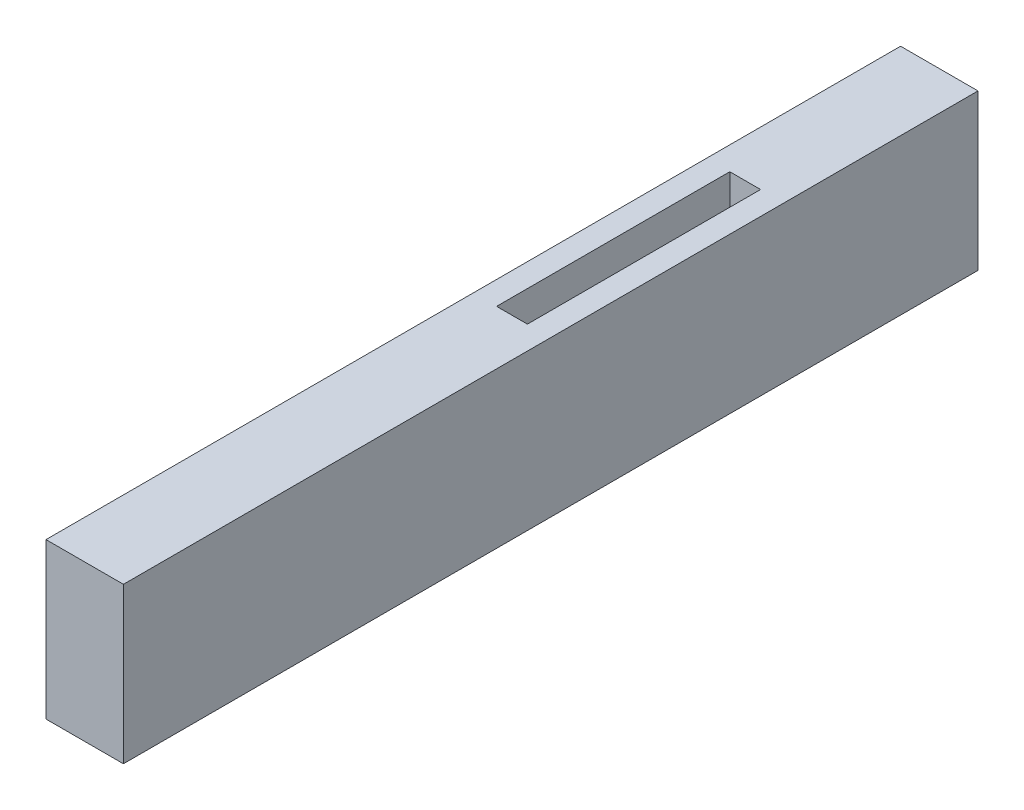
SolidWorks part; units mm, degrees
ref_plane "Front Plane" through (0, 0, 0) normal (0, 0, 1) x (1, 0, 0)
ref_plane "Top Plane" through (0, 0, 0) normal (0, 1, 0) x (1, 0, 0)
ref_plane "Right Plane" through (0, 0, 0) normal (1, 0, 0) x (0, 0, -1)
sketch "Sketch1" plane through (0, 0, 0) normal (0, 1, 0) x (1, 0, 0)
  line L0 (-14.2964, 30.5297) -> (-9.3157, 30.5297)
  line L1 (-9.3157, 30.5297) -> (-9.3157, -24.4422)
  line L2 (-9.3157, -24.4422) -> (-14.2964, -24.4422)
  line L3 (-14.2964, -24.4422) -> (-14.2964, 30.5297)
extrude "Boss-Extrude1" add sketch "Sketch1" along normal blind 10
sketch "Sketch2" plane through (0, 10, 0) normal (0, 1, 0) x (1, 0, 0)
  line L4 (-12.7964, 3.0437) -> (-10.8157, 3.0437)
  line L5 (-12.7964, 18.0437) -> (-10.8157, 18.0437)
  line L8 (-12.7964, 29.0297) -> (-12.7964, -22.9422)
  line L9 (-12.7964, -22.9422) -> (-10.8157, -22.9422)
  line L10 (-10.8157, -22.9422) -> (-10.8157, 29.0297)
  line L11 (-10.8157, 29.0297) -> (-12.7964, 29.0297)
  line L12 (-12.7964, 18.0437) -> (-12.7964, 3.0437)
  line L14 (-10.8157, 3.0437) -> (-10.8157, 18.0437)
  dimension "D1" = 1.5
extrude "Cut-Extrude2" cut sketch "Sketch2" against normal blind 7
sketch "Sketch4" plane through (0, 0, 0) normal (0, -1, 0) x (1, 0, 0)
  line L4 (-10.8157, -3.0437) -> (-12.7964, -3.0437)
  line L8 (-12.7964, 22.9422) -> (-12.7964, -29.0297)
  line L9 (-12.7964, -29.0297) -> (-10.8157, -29.0297)
  line L10 (-10.8157, -29.0297) -> (-10.8157, 22.9422)
  line L11 (-10.8157, 22.9422) -> (-12.7964, 22.9422)
  line L12 (-12.7964, 22.9422) -> (-12.7964, -3.0437)
  line L14 (-10.8157, -3.0437) -> (-10.8157, 22.9422)
  line L15 (-10.8157, 22.9422) -> (-12.7964, 22.9422)
  dimension "D1" = 1.5
extrude "Cut-Extrude3" cut sketch "Sketch4" against normal blind 7
